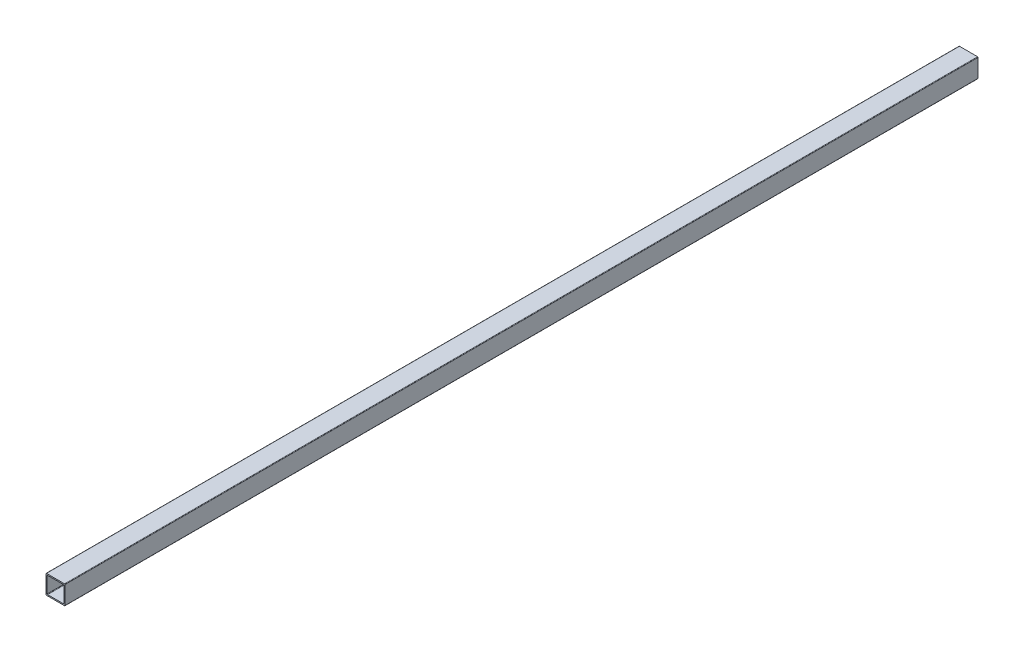
SolidWorks part; units mm, degrees
other "Camera1"
material "6061 Alloy"
ref_plane "Front Plane" through (0, 0, 0) normal (0, 0, 1) x (1, 0, 0)
ref_plane "Top Plane" through (0, 0, 0) normal (0, 1, 0) x (1, 0, 0)
ref_plane "Right Plane" through (0, 0, 0) normal (1, 0, 0) x (0, 0, -1)
sketch "Sketch1" plane through (0, 0, 0) normal (0, 1, 0) x (1, 0, 0)
  line L0 (0, 0) -> (0, -1219.2)
  dimension "D1" = 1219.2
other "Square tube 1 INCH SQUARE 0.0625 THICK(1)"
ref_plane "Plane1" through (0, 0, 0) normal (0, 0, 1) x (1, 0, 0)
sketch "Sketch2" plane through (0, 0, 0) normal (0, 0, 1) x (1, 0, 0)
  line L0 (-11.1125, -10.4775) -> (-11.1125, 10.4775)
  line L1 (12.065, -12.7) -> (-12.065, -12.7)
  line L2 (12.7, -12.065) -> (12.7, 12.065)
  line L3 (12.065, 12.7) -> (-12.065, 12.7)
  line L4 (-12.7, -12.065) -> (-12.7, 12.065)
  line L5 (12.7, -12.7) -> (-12.7, 12.7) construction
  line L6 (12.7, 12.7) -> (-12.7, -12.7) construction
  line L7 (10.4775, 11.1125) -> (-10.4775, 11.1125)
  line L8 (11.1125, -10.4775) -> (11.1125, 10.4775)
  line L9 (10.4775, -11.1125) -> (-10.4775, -11.1125)
  line L10 (-11.1125, -11.1125) -> (-11.1125, 11.1125) construction
  line L11 (11.1125, 11.1125) -> (-11.1125, 11.1125) construction
  line L12 (11.1125, -11.1125) -> (-11.1125, -11.1125) construction
  line L13 (11.1125, -11.1125) -> (11.1125, 11.1125) construction
  line L14 (12.7, -12.7) -> (-12.7, -12.7) construction
  line L15 (12.7, -12.7) -> (12.7, 12.7) construction
  line L16 (-12.7, -12.7) -> (-12.7, 12.7) construction
  line L17 (12.7, 12.7) -> (-12.7, 12.7) construction
  arc A0 (-11.1125, 10.4775) -> (-10.4775, 11.1125) centre (-10.4775, 10.4775) cw
  arc A1 (-11.1125, -10.4775) -> (-10.4775, -11.1125) centre (-10.4775, -10.4775) ccw
  arc A2 (11.1125, -10.4775) -> (10.4775, -11.1125) centre (10.4775, -10.4775) cw
  arc A3 (10.4775, 11.1125) -> (11.1125, 10.4775) centre (10.4775, 10.4775) cw
  arc A4 (12.065, -12.7) -> (12.7, -12.065) centre (12.065, -12.065) ccw
  arc A5 (-12.065, -12.7) -> (-12.7, -12.065) centre (-12.065, -12.065) cw
  arc A6 (12.7, 12.065) -> (12.065, 12.7) centre (12.065, 12.065) ccw
  arc A7 (-12.065, 12.7) -> (-12.7, 12.065) centre (-12.065, 12.065) ccw
  point P0 (0, 0)
  point P34 (0, 0)
  dimension "D3" = 0.635
  dimension "D1" = 25.4
  dimension "D2" = 1.5875
